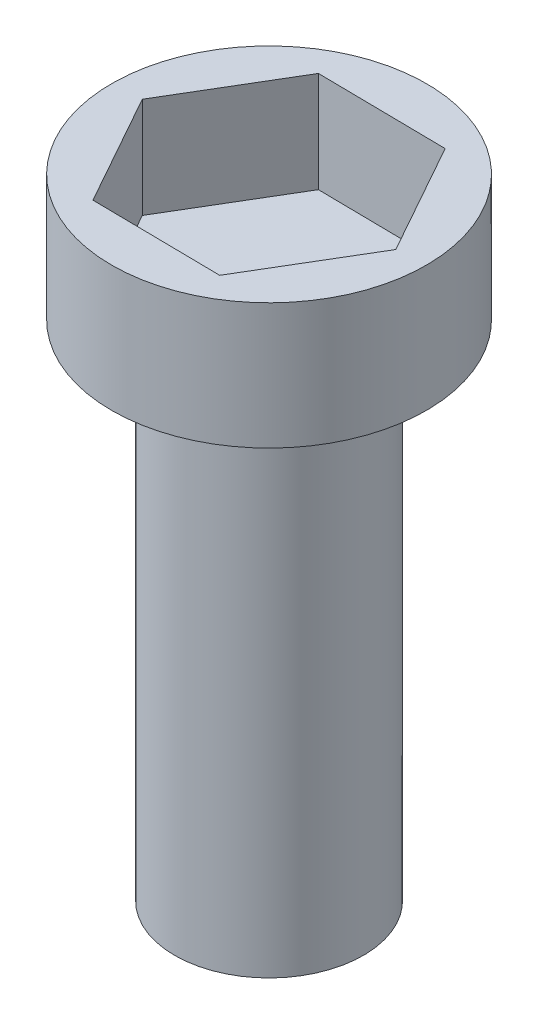
SolidWorks part; units mm, degrees
ref_plane "Front Plane" through (0, 0, 0) normal (0, 0, 1) x (1, 0, 0)
ref_plane "Top Plane" through (0, 0, 0) normal (0, 1, 0) x (1, 0, 0)
ref_plane "Right Plane" through (0, 0, 0) normal (1, 0, 0) x (0, 0, -1)
sketch "Sketch1" plane through (0, 0, 0) normal (0, 1, 0) x (1, 0, 0)
  circle A0 centre (0, 0) radius 1.5
  dimension "D1" = 3
extrude "Boss-Extrude1" add sketch "Sketch1" along normal blind 8
sketch "Sketch2" plane through (0, 8, 0) normal (0, 1, 0) x (1, 0, 0)
  circle A0 centre (0, 0) radius 2.5
  dimension "D1" = 5
extrude "Boss-Extrude2" add sketch "Sketch2" along normal blind 2
sketch "Sketch3" plane through (0, 10, 0) normal (0, 1, 0) x (1, 0, 0)
  line L1 (0.9971, -1.7816) -> (2.0414, -0.0273)
  line L2 (2.0414, -0.0273) -> (1.0443, 1.7543)
  line L3 (1.0443, 1.7543) -> (-0.9971, 1.7816)
  line L4 (-0.9971, 1.7816) -> (-2.0414, 0.0273)
  line L5 (-2.0414, 0.0273) -> (-1.0443, -1.7543)
  line L6 (-1.0443, -1.7543) -> (0.9971, -1.7816)
  circle A0 centre (0, 0) radius 1.7681 construction
extrude "Cut-Extrude2" cut sketch "Sketch3" against normal blind 1.6
